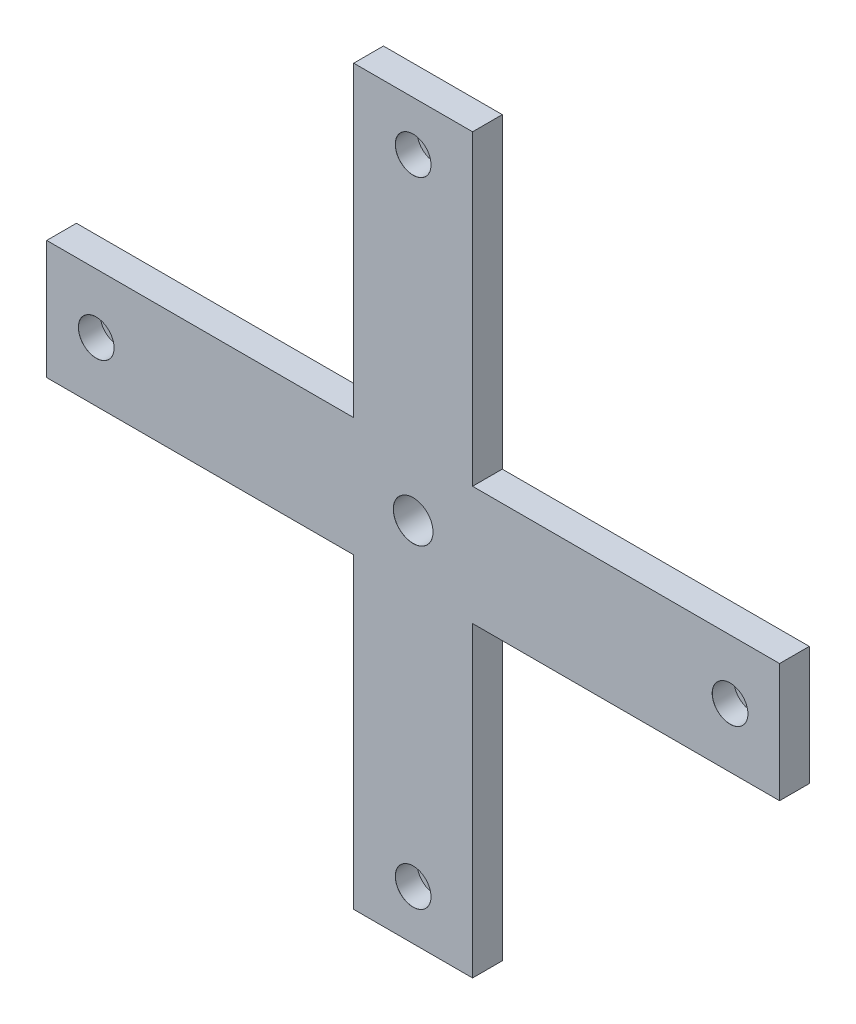
SolidWorks part; units mm, degrees
ref_plane "前视基准面" through (0, 0, 0) normal (0, 0, 1) x (1, 0, 0)
ref_plane "上视基准面" through (0, 0, 0) normal (0, 1, 0) x (1, 0, 0)
ref_plane "右视基准面" through (0, 0, 0) normal (1, 0, 0) x (0, 0, -1)
sketch "草图1" plane through (0, 0, 0) normal (0, 0, 1) x (1, 0, 0)
  line L1 (-185, 185) -> (185, 185)
  line L2 (-185, 185) -> (-185, -185)
  line L3 (-185, -185) -> (185, -185)
  line L4 (185, 185) -> (185, -185)
  line L5 (-185, 185) -> (185, -185) construction
  line L6 (-185, -185) -> (185, 185) construction
  point P0 (0, 0)
  dimension "D1" = 370
  dimension "D2" = 370
extrude "凸台-拉伸1" add sketch "草图1" along normal blind 15
sketch "草图2" plane through (0, 0, 15) normal (0, 0, 1) x (1, 0, 0)
  line L0 (-84.9122, 0) -> (102.1096, 0) construction
  line L1 (185, 185) -> (30, 185)
  line L2 (185, 185) -> (185, 30)
  line L3 (185, 30) -> (30, 30)
  line L4 (30, 185) -> (30, 30)
  line L5 (0, 47.8303) -> (0, -89.749) construction
  line L6 (-185, 30) -> (-30, 30)
  line L7 (-30, 185) -> (-30, 30)
  line L8 (-185, 185) -> (-30, 185)
  line L9 (-185, 185) -> (-185, 30)
  line L10 (-185, -185) -> (-185, -30)
  line L11 (-185, -185) -> (-30, -185)
  line L12 (-30, -185) -> (-30, -30)
  line L13 (-185, -30) -> (-30, -30)
  line L14 (30, -185) -> (30, -30)
  line L15 (185, -30) -> (30, -30)
  line L16 (185, -185) -> (185, -30)
  line L17 (185, -185) -> (30, -185)
  dimension "D1" = 60
  dimension "D2" = 60
extrude "切除-拉伸1" cut sketch "草图2" against normal blind 20
sketch "草图3" plane through (0, 0, 15) normal (0, 0, 1) x (1, 0, 0)
  line L2 (-160, 0) -> (160, 0)
  line L3 (0, 160) -> (0, -160)
  point P0 (0, 0)
  point P9 (0, 0)
  point P10 (0, 0)
  point P11 (0, 0)
  point P12 (0, 0)
  dimension "D1" = 320
  dimension "D2" = 320
  dimension "D3" = 160
  dimension "D4" = 160
hole_wizard "打孔尺寸(%根据)内六角圆柱头螺钉的类型1" positions "3D草图1" profile "草图4" counterbore size "M10" standard "GB"
sketch3d "3D草图1"
  point P0 (-160, 0, 15)
  point P3 (160, 0, 15)
  point P6 (0, 160, 15)
  point P9 (0, -160, 15)
sketch "草图4" plane through (-160, 0, 15) normal (1, 0, 0) x (0, -1, 0)
  line L0 (0, 0) -> (0, 20.3047)
  line L1 (0, 20.3047) -> (5.5, 17)
  line L2 (5.5, 17) -> (5.5, 11)
  line L3 (5.5, 11) -> (9, 11)
  line L5 (9, 11) -> (9, 0.025)
  line L6 (9, 0.025) -> (9.025, 0)
  line L7 (9.025, 0) -> (0, 0)
  line L8 (-9, 0.025) -> (-9.025, 0) construction
  line L10 (0, 20.3047) -> (-5.5, 17) construction
  line L11 (0, -6.35) -> (0, 107.95) construction
  dimension "孔直径" = 11
  dimension "孔深度" = 17
  dimension "锥形沉头孔直径" = 18
  dimension "锥形沉头孔深度" = 11
  dimension "近端锥形沉头孔直径" = 18.05
  dimension "近端锥形沉头孔角度" = 90
  dimension "导头角度" = 118
hole_wizard "大小mm 暗销槽口1" positions "草图5" profile "草图6" size "Ø20.0" standard "GB" slot yes
sketch "草图5" plane through (0, 0, 15) normal (0, 0, 1) x (1, 0, 0)
  point P0 (0, 0)
sketch "草图6" plane through (0, 0, 15) normal (1, 0, 0) x (0, -1, 0)
  line L0 (0, 0) -> (0, 23.0086)
  line L1 (0, 23.0086) -> (10, 17)
  line L2 (10, 17) -> (10, 0.025)
  line L3 (10, 0.025) -> (10.025, 0)
  line L5 (10.025, 0) -> (0, 0)
  line L6 (-10, 0.025) -> (-10.025, 0) construction
  line L10 (0, 23.0086) -> (-10, 17) construction
  line L11 (0, -6.35) -> (0, 107.95) construction
  dimension "孔直径" = 20
  dimension "孔深度" = 17
  dimension "近端锥形沉头孔直径" = 20.05
  dimension "近端锥形沉头孔角度" = 90
  dimension "导头角度" = 118
